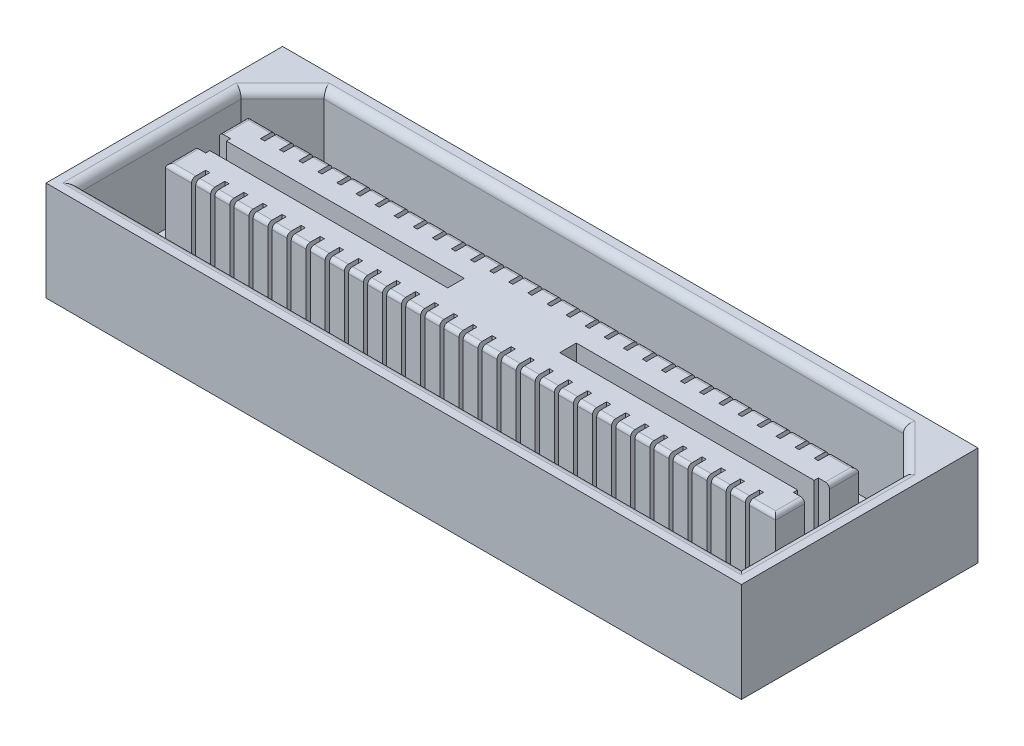
SolidWorks part; units mm, degrees
ref_plane "Front Plane" through (0, 0, 0) normal (0, 0, 1) x (1, 0, 0)
ref_plane "Top Plane" through (0, 0, 0) normal (0, 1, 0) x (1, 0, 0)
ref_plane "Right Plane" through (0, 0, 0) normal (1, 0, 0) x (0, 0, -1)
sketch "Sketch1" plane through (0, 0, 0) normal (0, 1, 0) x (1, 0, 0)
  line L1 (0, 0) -> (21.2776, 0)
  line L2 (0, 0) -> (0, 7.239)
  line L3 (0, 7.239) -> (21.2776, 7.239)
  line L4 (21.2776, 0) -> (21.2776, 7.239)
  dimension "D1" = 21.2776
  dimension "D2" = 7.239
extrude "Boss-Extrude1" add sketch "Sketch1" along normal blind 3.048
sketch "Sketch2" plane through (0, 3.048, 0) normal (0, 1, 0) x (1, 0, 0)
  line L0 (0.508, 5.461) -> (1.778, 6.731)
  line L1 (1.778, 6.731) -> (19.4996, 6.731)
  line L2 (0.508, 5.461) -> (0.508, 0.508)
  line L3 (0.508, 0.508) -> (20.7696, 0.508)
  line L4 (20.7696, 5.461) -> (20.7696, 0.508)
  line L5 (19.4996, 6.731) -> (20.7696, 5.461)
  line L6 (10.6388, 7.239) -> (10.6388, 6.731) construction
  line L7 (21.2776, 7.239) -> (0, 7.239) construction
  line L8 (0.508, 2.9845) -> (0, 2.9845) construction
  line L9 (0, 7.239) -> (0, 0) construction
  line L10 (10.6388, 0.508) -> (10.6388, 0) construction
  line L11 (0, 0) -> (21.2776, 0) construction
  line L12 (20.7696, 2.9845) -> (21.2776, 2.9845) construction
  line L15 (21.2776, 0) -> (21.2776, 7.239) construction
  line L16 (1.6472, 3.8735) -> (8.9243, 3.8735)
  line L17 (1.3043, 4.8895) -> (19.9733, 4.8895)
  line L18 (1.3043, 4.8895) -> (1.3043, 4.0005)
  line L19 (1.3043, 2.3495) -> (19.9733, 2.3495)
  line L20 (19.9733, 4.8895) -> (19.9733, 4.0005)
  line L21 (8.9243, 3.8735) -> (8.9243, 3.3655)
  line L22 (8.9243, 3.3655) -> (1.6472, 3.3655)
  line L23 (1.3043, 3.2385) -> (1.3043, 2.3495)
  line L24 (19.6304, 3.8735) -> (12.3533, 3.8735)
  line L25 (12.3533, 3.8735) -> (12.3533, 3.3655)
  line L26 (12.3533, 3.3655) -> (19.6304, 3.3655)
  line L27 (19.9733, 3.2385) -> (19.9733, 2.3495)
  line L28 (1.3043, 4.0005) -> (1.6472, 4.0005)
  line L29 (1.6472, 4.0005) -> (1.6472, 3.8735)
  line L30 (1.6472, 3.2385) -> (1.3043, 3.2385)
  line L31 (19.9733, 4.0005) -> (19.6304, 4.0005)
  line L32 (19.6304, 4.0005) -> (19.6304, 3.8735)
  line L33 (19.6304, 3.2385) -> (19.9733, 3.2385)
  line L34 (1.6472, 3.3655) -> (1.6472, 3.2385)
  line L35 (19.6304, 3.3655) -> (19.6304, 3.2385)
  line L36 (10.6388, 6.731) -> (10.6388, 0.508) construction
  line L37 (8.9243, 3.6195) -> (12.3533, 3.6195) construction
  point P44 (10.6388, 3.6195)
  point P45 (10.6388, 3.6195)
  dimension "D1" = 135
  dimension "D2" = 135
  dimension "D3" = 6.223
  dimension "D4" = 1.27
  dimension "D5" = 0.508
  dimension "D6" = 0.762
  dimension "D7" = 7.62
  dimension "D8" = 0.3429
  dimension "D9" = 3.429
  dimension "D10" = 2.54
extrude "Cut-Extrude1" cut sketch "Sketch2" against normal offset from surface (2.54 mm away) 0.508 up to face at (10.6388, 0, -3.6195)
fillet "Fillet1" radius 0.127 6 edges at (1.3043, 3.048, -4.445) (10.6388, 3.048, -4.8895) (19.9733, 3.048, -4.445) (19.9733, 3.048, -2.794) (1.3043, 3.048, -2.794) (10.6388, 3.048, -2.3495)
fillet "Fillet2" radius 0.254 6 edges at (20.7696, 3.048, -2.9845) (20.1346, 3.048, -6.096) (10.6388, 3.048, -0.508) (0.508, 3.048, -2.9845) (10.6388, 3.048, -6.731) (1.143, 3.048, -6.096)
sketch "Sketch3" plane through (0, 3.048, 0) normal (0, 1, 0) x (1, 0, 0)
  line L0 (2.6886, 2.7813) -> (2.6886, 2.1717)
  line L1 (2.1044, 2.7813) -> (2.2314, 2.7813)
  line L2 (2.1044, 2.7813) -> (2.1044, 2.1717)
  line L3 (2.1044, 2.1717) -> (2.2314, 2.1717)
  line L4 (2.2314, 2.7813) -> (2.2314, 2.1717)
  line L5 (2.6886, 2.7813) -> (2.8156, 2.7813)
  line L6 (2.8156, 2.7813) -> (2.8156, 2.1717)
  line L7 (2.6886, 2.1717) -> (2.8156, 2.1717)
  line L8 (3.2728, 2.7813) -> (3.2728, 2.1717)
  line L9 (3.2728, 2.7813) -> (3.3998, 2.7813)
  line L10 (3.3998, 2.7813) -> (3.3998, 2.1717)
  line L11 (3.2728, 2.1717) -> (3.3998, 2.1717)
  line L12 (3.857, 2.7813) -> (3.857, 2.1717)
  line L13 (3.857, 2.7813) -> (3.984, 2.7813)
  line L14 (3.984, 2.7813) -> (3.984, 2.1717)
  line L15 (3.857, 2.1717) -> (3.984, 2.1717)
  line L16 (4.4412, 2.7813) -> (4.4412, 2.1717)
  line L17 (4.4412, 2.7813) -> (4.5682, 2.7813)
  line L18 (4.5682, 2.7813) -> (4.5682, 2.1717)
  line L19 (4.4412, 2.1717) -> (4.5682, 2.1717)
  line L20 (5.0254, 2.7813) -> (5.0254, 2.1717)
  line L21 (5.0254, 2.7813) -> (5.1524, 2.7813)
  line L22 (5.1524, 2.7813) -> (5.1524, 2.1717)
  line L23 (5.0254, 2.1717) -> (5.1524, 2.1717)
  line L24 (5.6096, 2.7813) -> (5.6096, 2.1717)
  line L25 (5.6096, 2.7813) -> (5.7366, 2.7813)
  line L26 (5.7366, 2.7813) -> (5.7366, 2.1717)
  line L27 (5.6096, 2.1717) -> (5.7366, 2.1717)
  line L28 (6.1938, 2.7813) -> (6.1938, 2.1717)
  line L29 (6.1938, 2.7813) -> (6.3208, 2.7813)
  line L30 (6.3208, 2.7813) -> (6.3208, 2.1717)
  line L31 (6.1938, 2.1717) -> (6.3208, 2.1717)
  line L32 (6.778, 2.7813) -> (6.778, 2.1717)
  line L33 (6.778, 2.7813) -> (6.905, 2.7813)
  line L34 (6.905, 2.7813) -> (6.905, 2.1717)
  line L35 (6.778, 2.1717) -> (6.905, 2.1717)
  line L36 (7.3622, 2.7813) -> (7.3622, 2.1717)
  line L37 (7.3622, 2.7813) -> (7.4892, 2.7813)
  line L38 (7.4892, 2.7813) -> (7.4892, 2.1717)
  line L39 (7.3622, 2.1717) -> (7.4892, 2.1717)
  line L40 (7.9464, 2.7813) -> (7.9464, 2.1717)
  line L41 (7.9464, 2.7813) -> (8.0734, 2.7813)
  line L42 (8.0734, 2.7813) -> (8.0734, 2.1717)
  line L43 (7.9464, 2.1717) -> (8.0734, 2.1717)
  line L44 (8.5306, 2.7813) -> (8.5306, 2.1717)
  line L45 (8.5306, 2.7813) -> (8.6576, 2.7813)
  line L46 (8.6576, 2.7813) -> (8.6576, 2.1717)
  line L47 (8.5306, 2.1717) -> (8.6576, 2.1717)
  line L48 (9.1148, 2.7813) -> (9.1148, 2.1717)
  line L49 (9.1148, 2.7813) -> (9.2418, 2.7813)
  line L50 (9.2418, 2.7813) -> (9.2418, 2.1717)
  line L51 (9.1148, 2.1717) -> (9.2418, 2.1717)
  line L52 (9.699, 2.7813) -> (9.699, 2.1717)
  line L53 (9.699, 2.7813) -> (9.826, 2.7813)
  line L54 (9.826, 2.7813) -> (9.826, 2.1717)
  line L55 (9.699, 2.1717) -> (9.826, 2.1717)
  line L56 (10.2832, 2.7813) -> (10.2832, 2.1717)
  line L57 (10.2832, 2.7813) -> (10.4102, 2.7813)
  line L58 (10.4102, 2.7813) -> (10.4102, 2.1717)
  line L59 (10.2832, 2.1717) -> (10.4102, 2.1717)
  line L60 (10.8674, 2.7813) -> (10.8674, 2.1717)
  line L61 (10.8674, 2.7813) -> (10.9944, 2.7813)
  line L62 (10.9944, 2.7813) -> (10.9944, 2.1717)
  line L63 (10.8674, 2.1717) -> (10.9944, 2.1717)
  line L64 (11.4516, 2.7813) -> (11.4516, 2.1717)
  line L65 (11.4516, 2.7813) -> (11.5786, 2.7813)
  line L66 (11.5786, 2.7813) -> (11.5786, 2.1717)
  line L67 (11.4516, 2.1717) -> (11.5786, 2.1717)
  line L68 (12.0358, 2.7813) -> (12.0358, 2.1717)
  line L69 (12.0358, 2.7813) -> (12.1628, 2.7813)
  line L70 (12.1628, 2.7813) -> (12.1628, 2.1717)
  line L71 (12.0358, 2.1717) -> (12.1628, 2.1717)
  line L72 (12.62, 2.7813) -> (12.62, 2.1717)
  line L73 (12.62, 2.7813) -> (12.747, 2.7813)
  line L74 (12.747, 2.7813) -> (12.747, 2.1717)
  line L75 (12.62, 2.1717) -> (12.747, 2.1717)
  line L76 (13.2042, 2.7813) -> (13.2042, 2.1717)
  line L77 (13.2042, 2.7813) -> (13.3312, 2.7813)
  line L78 (13.3312, 2.7813) -> (13.3312, 2.1717)
  line L79 (13.2042, 2.1717) -> (13.3312, 2.1717)
  line L80 (13.7884, 2.7813) -> (13.7884, 2.1717)
  line L81 (13.7884, 2.7813) -> (13.9154, 2.7813)
  line L82 (13.9154, 2.7813) -> (13.9154, 2.1717)
  line L83 (13.7884, 2.1717) -> (13.9154, 2.1717)
  line L84 (14.3726, 2.7813) -> (14.3726, 2.1717)
  line L85 (14.3726, 2.7813) -> (14.4996, 2.7813)
  line L86 (14.4996, 2.7813) -> (14.4996, 2.1717)
  line L87 (14.3726, 2.1717) -> (14.4996, 2.1717)
  line L88 (14.9568, 2.7813) -> (14.9568, 2.1717)
  line L89 (14.9568, 2.7813) -> (15.0838, 2.7813)
  line L90 (15.0838, 2.7813) -> (15.0838, 2.1717)
  line L91 (14.9568, 2.1717) -> (15.0838, 2.1717)
  line L92 (15.541, 2.7813) -> (15.541, 2.1717)
  line L93 (15.541, 2.7813) -> (15.668, 2.7813)
  line L94 (15.668, 2.7813) -> (15.668, 2.1717)
  line L95 (15.541, 2.1717) -> (15.668, 2.1717)
  line L96 (16.1252, 2.7813) -> (16.1252, 2.1717)
  line L97 (16.1252, 2.7813) -> (16.2522, 2.7813)
  line L98 (16.2522, 2.7813) -> (16.2522, 2.1717)
  line L99 (16.1252, 2.1717) -> (16.2522, 2.1717)
  line L100 (16.7094, 2.7813) -> (16.7094, 2.1717)
  line L101 (16.7094, 2.7813) -> (16.8364, 2.7813)
  line L102 (16.8364, 2.7813) -> (16.8364, 2.1717)
  line L103 (16.7094, 2.1717) -> (16.8364, 2.1717)
  line L104 (17.2936, 2.7813) -> (17.2936, 2.1717)
  line L105 (17.2936, 2.7813) -> (17.4206, 2.7813)
  line L106 (17.4206, 2.7813) -> (17.4206, 2.1717)
  line L107 (17.2936, 2.1717) -> (17.4206, 2.1717)
  line L108 (17.8778, 2.7813) -> (17.8778, 2.1717)
  line L109 (17.8778, 2.7813) -> (18.0048, 2.7813)
  line L110 (18.0048, 2.7813) -> (18.0048, 2.1717)
  line L111 (17.8778, 2.1717) -> (18.0048, 2.1717)
  line L112 (18.462, 2.7813) -> (18.462, 2.1717)
  line L113 (18.462, 2.7813) -> (18.589, 2.7813)
  line L114 (18.589, 2.7813) -> (18.589, 2.1717)
  line L115 (18.462, 2.1717) -> (18.589, 2.1717)
  line L116 (19.0462, 2.7813) -> (19.0462, 2.1717)
  line L117 (19.0462, 2.7813) -> (19.1732, 2.7813)
  line L118 (19.1732, 2.7813) -> (19.1732, 2.1717)
  line L119 (19.0462, 2.1717) -> (19.1732, 2.1717)
  line L120 (8.9243, 3.3655) -> (1.6472, 3.3655) construction
  line L121 (10.4102, 2.7813) -> (10.8674, 2.7813) construction
  line L122 (0, 0) -> (21.2776, 0) construction
  line L123 (10.6388, 0) -> (10.6388, 7.239) construction
  line L124 (21.2776, 7.239) -> (0, 7.239) construction
  line L125 (10.4102, 4.4577) -> (10.8674, 4.4577) construction
  line L126 (19.0462, 5.0673) -> (19.1732, 5.0673)
  line L127 (0, 3.6195) -> (21.2776, 3.6195) construction
  line L128 (0, 7.239) -> (0, 0) construction
  line L129 (21.2776, 0) -> (21.2776, 7.239) construction
  line L130 (19.1732, 4.4577) -> (19.1732, 5.0673)
  line L131 (19.0462, 4.4577) -> (19.1732, 4.4577)
  line L132 (19.0462, 4.4577) -> (19.0462, 5.0673)
  line L133 (18.462, 5.0673) -> (18.589, 5.0673)
  line L134 (18.589, 4.4577) -> (18.589, 5.0673)
  line L135 (18.462, 4.4577) -> (18.589, 4.4577)
  line L136 (18.462, 4.4577) -> (18.462, 5.0673)
  line L137 (17.8778, 5.0673) -> (18.0048, 5.0673)
  line L138 (18.0048, 4.4577) -> (18.0048, 5.0673)
  line L139 (17.8778, 4.4577) -> (18.0048, 4.4577)
  line L140 (17.8778, 4.4577) -> (17.8778, 5.0673)
  line L141 (17.2936, 5.0673) -> (17.4206, 5.0673)
  line L142 (17.4206, 4.4577) -> (17.4206, 5.0673)
  line L143 (17.2936, 4.4577) -> (17.4206, 4.4577)
  line L144 (17.2936, 4.4577) -> (17.2936, 5.0673)
  line L145 (16.7094, 5.0673) -> (16.8364, 5.0673)
  line L146 (16.8364, 4.4577) -> (16.8364, 5.0673)
  line L147 (16.7094, 4.4577) -> (16.8364, 4.4577)
  line L148 (16.7094, 4.4577) -> (16.7094, 5.0673)
  line L149 (16.1252, 5.0673) -> (16.2522, 5.0673)
  line L150 (16.2522, 4.4577) -> (16.2522, 5.0673)
  line L151 (16.1252, 4.4577) -> (16.2522, 4.4577)
  line L152 (16.1252, 4.4577) -> (16.1252, 5.0673)
  line L153 (15.541, 5.0673) -> (15.668, 5.0673)
  line L154 (15.668, 4.4577) -> (15.668, 5.0673)
  line L155 (15.541, 4.4577) -> (15.668, 4.4577)
  line L156 (15.541, 4.4577) -> (15.541, 5.0673)
  line L157 (14.9568, 5.0673) -> (15.0838, 5.0673)
  line L158 (15.0838, 4.4577) -> (15.0838, 5.0673)
  line L159 (14.9568, 4.4577) -> (15.0838, 4.4577)
  line L160 (14.9568, 4.4577) -> (14.9568, 5.0673)
  line L161 (14.3726, 5.0673) -> (14.4996, 5.0673)
  line L162 (14.4996, 4.4577) -> (14.4996, 5.0673)
  line L163 (14.3726, 4.4577) -> (14.4996, 4.4577)
  line L164 (14.3726, 4.4577) -> (14.3726, 5.0673)
  line L165 (13.7884, 5.0673) -> (13.9154, 5.0673)
  line L166 (13.9154, 4.4577) -> (13.9154, 5.0673)
  line L167 (13.7884, 4.4577) -> (13.9154, 4.4577)
  line L168 (13.7884, 4.4577) -> (13.7884, 5.0673)
  line L169 (13.2042, 5.0673) -> (13.3312, 5.0673)
  line L170 (13.3312, 4.4577) -> (13.3312, 5.0673)
  line L171 (13.2042, 4.4577) -> (13.3312, 4.4577)
  line L172 (13.2042, 4.4577) -> (13.2042, 5.0673)
  line L173 (12.62, 5.0673) -> (12.747, 5.0673)
  line L174 (12.747, 4.4577) -> (12.747, 5.0673)
  line L175 (12.62, 4.4577) -> (12.747, 4.4577)
  line L176 (12.62, 4.4577) -> (12.62, 5.0673)
  line L177 (12.0358, 5.0673) -> (12.1628, 5.0673)
  line L178 (12.1628, 4.4577) -> (12.1628, 5.0673)
  line L179 (12.0358, 4.4577) -> (12.1628, 4.4577)
  line L180 (12.0358, 4.4577) -> (12.0358, 5.0673)
  line L181 (11.4516, 5.0673) -> (11.5786, 5.0673)
  line L182 (11.5786, 4.4577) -> (11.5786, 5.0673)
  line L183 (11.4516, 4.4577) -> (11.5786, 4.4577)
  line L184 (11.4516, 4.4577) -> (11.4516, 5.0673)
  line L185 (10.8674, 5.0673) -> (10.9944, 5.0673)
  line L186 (10.9944, 4.4577) -> (10.9944, 5.0673)
  line L187 (10.8674, 4.4577) -> (10.9944, 4.4577)
  line L188 (10.8674, 4.4577) -> (10.8674, 5.0673)
  line L189 (10.2832, 5.0673) -> (10.4102, 5.0673)
  line L190 (10.4102, 4.4577) -> (10.4102, 5.0673)
  line L191 (10.2832, 4.4577) -> (10.4102, 4.4577)
  line L192 (10.2832, 4.4577) -> (10.2832, 5.0673)
  line L193 (9.699, 5.0673) -> (9.826, 5.0673)
  line L194 (9.826, 4.4577) -> (9.826, 5.0673)
  line L195 (9.699, 4.4577) -> (9.826, 4.4577)
  line L196 (9.699, 4.4577) -> (9.699, 5.0673)
  line L197 (9.1148, 5.0673) -> (9.2418, 5.0673)
  line L198 (9.2418, 4.4577) -> (9.2418, 5.0673)
  line L199 (9.1148, 4.4577) -> (9.2418, 4.4577)
  line L200 (9.1148, 4.4577) -> (9.1148, 5.0673)
  line L201 (8.5306, 5.0673) -> (8.6576, 5.0673)
  line L202 (8.6576, 4.4577) -> (8.6576, 5.0673)
  line L203 (8.5306, 4.4577) -> (8.6576, 4.4577)
  line L204 (8.5306, 4.4577) -> (8.5306, 5.0673)
  line L205 (7.9464, 5.0673) -> (8.0734, 5.0673)
  line L206 (8.0734, 4.4577) -> (8.0734, 5.0673)
  line L207 (7.9464, 4.4577) -> (8.0734, 4.4577)
  line L208 (7.9464, 4.4577) -> (7.9464, 5.0673)
  line L209 (7.3622, 5.0673) -> (7.4892, 5.0673)
  line L210 (7.4892, 4.4577) -> (7.4892, 5.0673)
  line L211 (7.3622, 4.4577) -> (7.4892, 4.4577)
  line L212 (7.3622, 4.4577) -> (7.3622, 5.0673)
  line L213 (6.778, 5.0673) -> (6.905, 5.0673)
  line L214 (6.905, 4.4577) -> (6.905, 5.0673)
  line L215 (6.778, 4.4577) -> (6.905, 4.4577)
  line L216 (6.778, 4.4577) -> (6.778, 5.0673)
  line L217 (6.1938, 5.0673) -> (6.3208, 5.0673)
  line L218 (6.3208, 4.4577) -> (6.3208, 5.0673)
  line L219 (6.1938, 4.4577) -> (6.3208, 4.4577)
  line L220 (6.1938, 4.4577) -> (6.1938, 5.0673)
  line L221 (5.6096, 5.0673) -> (5.7366, 5.0673)
  line L222 (5.7366, 4.4577) -> (5.7366, 5.0673)
  line L223 (5.6096, 4.4577) -> (5.7366, 4.4577)
  line L224 (5.6096, 4.4577) -> (5.6096, 5.0673)
  line L225 (5.0254, 5.0673) -> (5.1524, 5.0673)
  line L226 (5.1524, 4.4577) -> (5.1524, 5.0673)
  line L227 (5.0254, 4.4577) -> (5.1524, 4.4577)
  line L228 (5.0254, 4.4577) -> (5.0254, 5.0673)
  line L229 (4.4412, 5.0673) -> (4.5682, 5.0673)
  line L230 (4.5682, 4.4577) -> (4.5682, 5.0673)
  line L231 (4.4412, 4.4577) -> (4.5682, 4.4577)
  line L232 (4.4412, 4.4577) -> (4.4412, 5.0673)
  line L233 (3.857, 5.0673) -> (3.984, 5.0673)
  line L234 (3.984, 4.4577) -> (3.984, 5.0673)
  line L235 (3.857, 4.4577) -> (3.984, 4.4577)
  line L236 (3.857, 4.4577) -> (3.857, 5.0673)
  line L237 (3.2728, 5.0673) -> (3.3998, 5.0673)
  line L238 (3.3998, 4.4577) -> (3.3998, 5.0673)
  line L239 (3.2728, 4.4577) -> (3.3998, 4.4577)
  line L240 (3.2728, 4.4577) -> (3.2728, 5.0673)
  line L241 (2.6886, 5.0673) -> (2.8156, 5.0673)
  line L242 (2.8156, 4.4577) -> (2.8156, 5.0673)
  line L243 (2.6886, 4.4577) -> (2.8156, 4.4577)
  line L244 (2.2314, 4.4577) -> (2.2314, 5.0673)
  line L245 (2.1044, 5.0673) -> (2.2314, 5.0673)
  line L246 (2.1044, 4.4577) -> (2.1044, 5.0673)
  line L247 (2.1044, 4.4577) -> (2.2314, 4.4577)
  line L248 (2.6886, 4.4577) -> (2.6886, 5.0673)
  point P122 (10.6388, 2.7813)
  dimension "D1" = 0.6096
  dimension "D2" = 0.127
  dimension "D4" = 0.5842
  dimension "D5" = 0.5842
  dimension "D3" = 30
extrude "Cut-Extrude2" cut sketch "Sketch3" against normal up to surface (3.048 mm away) up to face at (10.6388, 0, -3.6195)
sketch "Sketch4" plane through (0, 0, 0) normal (0, -1, 0) x (1, 0, 0)
  line L0 (0, 0) -> (21.2776, 0) construction
  line L1 (21.2738, -7.2395) -> (0.0038, -7.2395)
  line L2 (21.2738, -7.2395) -> (21.2738, 0.0005)
  line L3 (21.2738, 0.0005) -> (0.0038, 0.0005)
  line L4 (0.0038, -7.2395) -> (0.0038, 0.0005)
  line L5 (21.2738, -7.2395) -> (0.0038, 0.0005) construction
  line L6 (21.2738, 0.0005) -> (0.0038, -7.2395) construction
  line L7 (0, -7.239) -> (0, 0) construction
  point P0 (10.6388, -3.6195)
  point P7 (10.6388, 0)
  point P10 (0, -3.6195)
  dimension "D1" = 7.24
  dimension "D2" = 21.27
